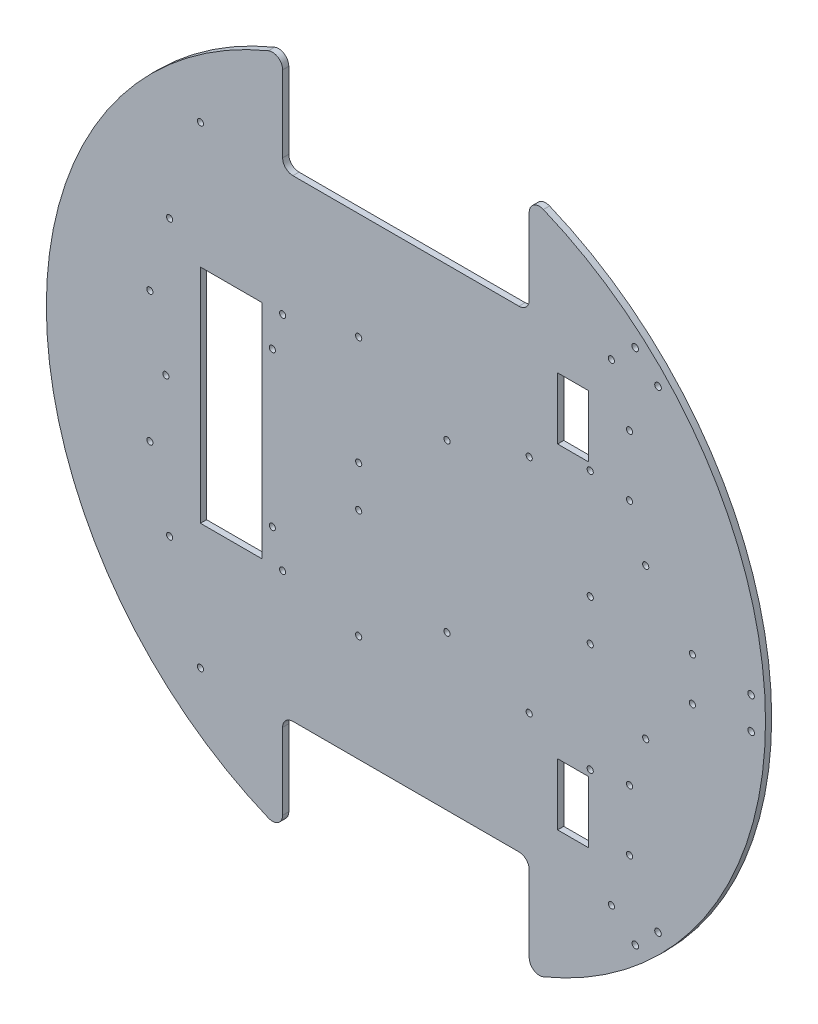
SolidWorks part; units mm, degrees
material "ｱｸﾘﾙ (中-上級の耐衝撃性)"
ref_plane "正面" through (0, 0, 0) normal (0, 0, 1) x (1, 0, 0)
ref_plane "平面" through (0, 0, 0) normal (0, 1, 0) x (1, 0, 0)
ref_plane "右側面" through (0, 0, 0) normal (1, 0, 0) x (0, 0, -1)
sketch "ｽｹｯﾁ1" plane through (0, 0, 0) normal (0, 0, 1) x (1, 0, 0)
  circle A0 centre (0, 0) radius 175
  dimension "D1" = 350
extrude "ﾎﾞｽ - 押し出し1" add sketch "ｽｹｯﾁ1" along normal blind 3
sketch "ｽｹｯﾁ2" plane through (0, 0, 3) normal (0, 0, 1) x (1, 0, 0)
  line L0 (0, 0) -> (175, 0)
  line L1 (0, 0) -> (-175, 0)
  line L2 (0, 0) -> (0, 115)
  line L3 (0, 0) -> (0, -115)
  line L4 (0, 115) -> (60, 115)
  line L5 (0, 115) -> (0, 175)
  line L6 (0, 175) -> (60, 175)
  line L7 (60, 115) -> (60, 175)
  line L8 (0, 115) -> (-60, 115)
  line L9 (0, 115) -> (0, 175)
  line L10 (0, 175) -> (-60, 175)
  line L11 (-60, 115) -> (-60, 175)
  line L13 (0, -115) -> (60, -115)
  line L14 (0, -115) -> (0, -175)
  line L15 (0, -175) -> (60, -175)
  line L16 (60, -115) -> (60, -175)
  line L17 (0, -115) -> (-60, -115)
  line L18 (0, -115) -> (0, -175)
  line L19 (0, -175) -> (-60, -175)
  line L20 (-60, -115) -> (-60, -175)
  circle A0 centre (0, 0) radius 175 construction
  circle M1 centre (0, 0) radius 175
  dimension "D1" = 115
  dimension "D2" = 60
  dimension "D3" = 60
  dimension "D4" = 60
  dimension "D5" = 115
  dimension "D6" = 60
extrude "ｶｯﾄ - 押し出し1" cut sketch "ｽｹｯﾁ2" against normal blind 3 contours L11 L8 L5 M1 | L4 L7 L5 M1 | L17 L20 L14 M1 | L16 L13 L14 M1
fillet "ﾌｨﾚｯﾄ1" radius 5 1 edges at (-60, 164.3928, 1.5)
fillet "ﾌｨﾚｯﾄ2" radius 5 3 edges at (60, 115, 1.5) (60, 164.3928, 1.5) (-60, 115, 1.5)
fillet "ﾌｨﾚｯﾄ3" radius 5 4 edges at (-60, -164.3928, 1.5) (-60, -115, 1.5) (60, -164.3928, 1.5) (60, -115, 1.5)
sketch "ｽｹｯﾁ5" plane through (0, 0, 3) normal (0, 0, 1) x (1, 0, 0)
  line L0 (0, 115) -> (-100, 115)
  line L1 (55, 115) -> (-55, 115) construction
  line L2 (0, 115) -> (100, 115)
  line L3 (0, -115) -> (100, -115)
  line L4 (55, -115) -> (-55, -115) construction
  line L5 (100, -115) -> (-100, -115)
  circle A0 centre (-100, -115) radius 1.5
  circle A1 centre (100, -115) radius 1.5
  circle A2 centre (100, 115) radius 1.5
  circle A3 centre (-100, 115) radius 1.5
  dimension "D3" = 3
  dimension "D4" = 3
  dimension "D5" = 3
  dimension "D6" = 3
  dimension "D1" = 100
  dimension "D2" = 100
extrude "ｶｯﾄ - 押し出し4" cut sketch "ｽｹｯﾁ5" against normal blind 3 contours A1 | A0 | A3 | A2
sketch "ｽｹｯﾁ6" plane through (0, 0, 3) normal (0, 0, 1) x (1, 0, 0)
  line L1 (-60, 54) -> (60, 54)
  line L2 (-60, 54) -> (-60, -54)
  line L3 (-60, -54) -> (60, -54)
  line L4 (60, 54) -> (60, -54)
  line L5 (-60, 54) -> (60, -54) construction
  line L6 (-60, -54) -> (60, 54) construction
  circle A0 centre (-60, 54) radius 1.5
  circle A1 centre (60, 54) radius 1.5
  circle A2 centre (-60, -54) radius 1.5
  circle A3 centre (60, -54) radius 1.5
  point P0 (0, 0)
  dimension "D3" = 3
  dimension "D4" = 3
  dimension "D5" = 3
  dimension "D6" = 3
  dimension "D1" = 120
  dimension "D2" = 108
extrude "ｶｯﾄ - 押し出し5" cut sketch "ｽｹｯﾁ6" against normal blind 3 contours A2 | A0 | A1 | A3
sketch "ｽｹｯﾁ7" plane through (0, 0, 3) normal (0, 0, 1) x (1, 0, 0)
  line L0 (-60, -54) -> (-70, -54)
  line L2 (-70, -54) -> (-100, -54)
  line L3 (-70, -54) -> (-70, 54)
  line L4 (-70, 54) -> (-100, 54)
  line L5 (-100, -54) -> (-100, 54)
  dimension "D1" = 10
  dimension "D2" = 108
  dimension "D3" = 30
extrude "ｶｯﾄ - 押し出し6" cut sketch "ｽｹｯﾁ7" against normal blind 3 contours L5 L2 L3 L4
sketch "ｽｹｯﾁ8" plane through (0, 0, 3) normal (0, 0, 1) x (1, 0, 0)
  line L0 (-100, 0) -> (-115, 0)
  line L1 (-100, -54) -> (-100, 54) construction
  line L2 (-115, 0) -> (-115, 67)
  line L3 (-115, 0) -> (-115, -67)
  circle A0 centre (-115, -67) radius 1.5
  circle A1 centre (-116.8225, 0) radius 1.5
  circle A2 centre (-115, 67) radius 1.5
  dimension "D4" = 3
  dimension "D5" = 3
  dimension "D6" = 3
  dimension "D1" = 15
  dimension "D2" = 67
  dimension "D3" = 67
extrude "ｶｯﾄ - 押し出し7" cut sketch "ｽｹｯﾁ8" against normal blind 3 contours A2 | A1 | A0
sketch "ｽｹｯﾁ9" plane through (0, 0, 3) normal (0, 0, 1) x (1, 0, 0)
  line L0 (-70, 0) -> (-65, 0)
  line L1 (-70, -54) -> (-70, 54) construction
  line L2 (-65, 0) -> (-65, 37)
  line L3 (-65, 37) -> (-64.7716, 37.1905)
  line L4 (-65, 0) -> (-65, -38)
  line L5 (-65, 0) -> (20, 0)
  line L6 (20, 0) -> (20, 41)
  line L7 (20, 0) -> (20, -40)
  circle A0 centre (-65, 37) radius 1.5
  circle A1 centre (20, 41) radius 1.5
  circle A2 centre (-65, -38) radius 1.5
  circle A3 centre (20, -40) radius 1.5
  dimension "D7" = 3
  dimension "D8" = 3
  dimension "D9" = 3
  dimension "D10" = 3
  dimension "D1" = 5
  dimension "D2" = 37
  dimension "D3" = 38
  dimension "D4" = 85
  dimension "D5" = 41
  dimension "D6" = 40
extrude "ｶｯﾄ - 押し出し8" cut sketch "ｽｹｯﾁ9" against normal blind 10 contours A0 | A2 | A1 | A3
sketch "ｽｹｯﾁ10" plane through (0, 0, 3) normal (0, 0, 1) x (1, 0, 0)
  line L0 (0, 0) -> (152.2366, 0)
  line L1 (0, 0) -> (66.9742, 68.8711)
  line L2 (0, 0) -> (76.2283, -78.3873)
  line L3 (175, 0) -> (168, 0)
  line L4 (-175, 0) -> (-168, 0)
  line L5 (66.9742, 68.8711) -> (117.1237, 120.441)
  line L6 (76.2283, -78.3873) -> (117.1237, -120.441)
  line L7 (117.1237, -120.441) -> (122.6798, -115.038)
  line L8 (117.1237, -120.441) -> (111.6437, -125.9211)
  line L9 (168, 0) -> (168, 7.75)
  line L10 (168, 0) -> (168, -7.75)
  line L11 (117.1237, 120.441) -> (111.5677, 125.844)
  line L12 (117.1237, 120.441) -> (122.6798, 115.038)
  arc A0 (66.9118, -161.7029) -> (66.9118, 161.7029) centre (0, 0) ccw construction
  arc A1 (-66.9118, 161.7029) -> (-66.9118, -161.7029) centre (0, 0) ccw construction
  circle A2 centre (0, 0) radius 168
  circle A3 centre (111.6437, -125.9211) radius 1.6
  circle A4 centre (122.6798, -115.038) radius 1.6
  circle A5 centre (168, 7.75) radius 1.6
  circle A6 centre (168, -7.75) radius 1.6
  circle A7 centre (111.5677, 125.844) radius 1.6
  circle A8 centre (122.6798, 115.038) radius 1.6
  dimension "D7" = 3.2
  dimension "D8" = 3.2
  dimension "D11" = 3.2
  dimension "D12" = 3.2
  dimension "D15" = 3.2
  dimension "D16" = 3.2
  dimension "D1" = 45.8
  dimension "D2" = 45.8
  dimension "D3" = 7
  dimension "D4" = 7
  dimension "D5" = 7.75
  dimension "D6" = 7.75
  dimension "D9" = 7.75
  dimension "D10" = 7.75
  dimension "D13" = 7.75
  dimension "D14" = 7.75
extrude "ｶｯﾄ - 押し出し9" cut sketch "ｽｹｯﾁ10" against normal blind 10 contours A3 | A4 | A6 | A5 | A7 | A8
sketch "ｽｹｯﾁ11" plane through (0, 0, 3) normal (0, 0, 1) x (1, 0, 0)
  line L0 (0, 0) -> (115, 0)
  line L1 (0, 0) -> (81.3173, 81.3173)
  line L2 (0, 0) -> (81.3173, -81.3173)
  line L4 (73.8173, 96.3173) -> (88.8173, 96.3173)
  line L5 (73.8173, 96.3173) -> (73.8173, 66.3173)
  line L6 (73.8173, 66.3173) -> (88.8173, 66.3173)
  line L7 (88.8173, 96.3173) -> (88.8173, 66.3173)
  line L8 (73.8173, 96.3173) -> (88.8173, 66.3173) construction
  line L9 (73.8173, 66.3173) -> (88.8173, 96.3173) construction
  line L10 (73.8173, -66.3173) -> (88.8173, -66.3173)
  line L11 (73.8173, -66.3173) -> (73.8173, -96.3173)
  line L12 (73.8173, -96.3173) -> (88.8173, -96.3173)
  line L13 (88.8173, -66.3173) -> (88.8173, -96.3173)
  line L14 (73.8173, -66.3173) -> (88.8173, -96.3173) construction
  line L15 (73.8173, -96.3173) -> (88.8173, -66.3173) construction
  circle A0 centre (0, 0) radius 115
  dimension "D1" = 230
  dimension "D2" = 45
  dimension "D3" = 45
  dimension "D4" = 30
  dimension "D5" = 15
  dimension "D6" = 15
  dimension "D7" = 30
extrude "ｶｯﾄ - 押し出し10" cut sketch "ｽｹｯﾁ11" against normal blind 10 contours L7 L6 L5 L4 | L13 L12 L11 L10
sketch "ｽｹｯﾁ12" plane through (0, 0, 3) normal (0, 0, 1) x (1, 0, 0)
  circle A3 centre (139.4, 10.5) radius 1.5
  circle A4 centre (139.4, -10.5) radius 1.5
  dimension "D4" = 3
  dimension "D1" = 21
extrude "ｶｯﾄ - 押し出し11" cut sketch "ｽｹｯﾁ12" against normal through all
sketch "ｽｹｯﾁ13" plane through (0, 0, 3) normal (0, 0, 1) x (1, 0, 0)
  line L0 (175, 0) -> (-70, 0) construction
  line L1 (-70, -54) -> (-70, 54) construction
  line L2 (89.6921, 61.5) -> (89.6921, 11.5) construction
  arc A0 (66.9118, -161.7029) -> (66.9118, 161.7029) centre (0, 0) ccw construction
  circle A1 centre (89.6921, 10) radius 1.5
  circle A2 centre (89.6921, 63) radius 1.5
  circle A3 centre (-22.9884, 63) radius 1.5
  circle A4 centre (-22.9884, 10) radius 1.5
  circle A5 centre (116.6921, 36.5) radius 1.5
  dimension "D1" = 3
  dimension "D2" = 10
  dimension "D3" = 3
  dimension "D4" = 53
  dimension "D5" = 3
  dimension "D6" = 3
  dimension "D7" = 27
  dimension "D8" = 3
extrude "ｶｯﾄ - 押し出し12" cut sketch "ｽｹｯﾁ13" against normal through all
pattern_linear "直線ﾊﾟﾀｰﾝ1" count 2 spacing 73 along (0, -1, 0) of "ｶｯﾄ - 押し出し12"
sketch "ｽｹｯﾁ14" plane through (0, 0, 3) normal (0, 0, 1) x (1, 0, 0)
  line L0 (175, 0) -> (98.9957, 0) construction
  arc A0 (66.9118, -161.7029) -> (66.9118, 161.7029) centre (0, 0) ccw construction
  circle A1 centre (108.8173, 89.5) radius 1.5
  circle A2 centre (108.8173, 60) radius 1.5
  dimension "D1" = 60
  dimension "D2" = 3
  dimension "D3" = 3
  dimension "D4" = 29.5
extrude "ｶｯﾄ - 押し出し14" cut sketch "ｽｹｯﾁ14" against normal through all
sketch "ｽｹｯﾁ17" plane through (0, 0, 3) normal (0, 0, 1) x (1, 0, 0)
  circle A2 centre (108.8173, -60) radius 1.5
  circle A3 centre (108.8173, -89.5) radius 1.5
  dimension "D2" = 3
  dimension "D3" = 3
  dimension "D4" = 29.5
extrude "ｶｯﾄ - 押し出し15" cut sketch "ｽｹｯﾁ17" against normal through all
sketch "ｽｹｯﾁ18" plane through (0, 0, 3) normal (0, 0, 1) x (1, 0, 0)
  circle A0 centre (-124.6106, 31.75) radius 1.5
  circle A1 centre (-124.6106, -31.75) radius 1.5
  dimension "D3" = 3
  dimension "D4" = 3
extrude "ｶｯﾄ - 押し出し16" cut sketch "ｽｹｯﾁ18" against normal through all
